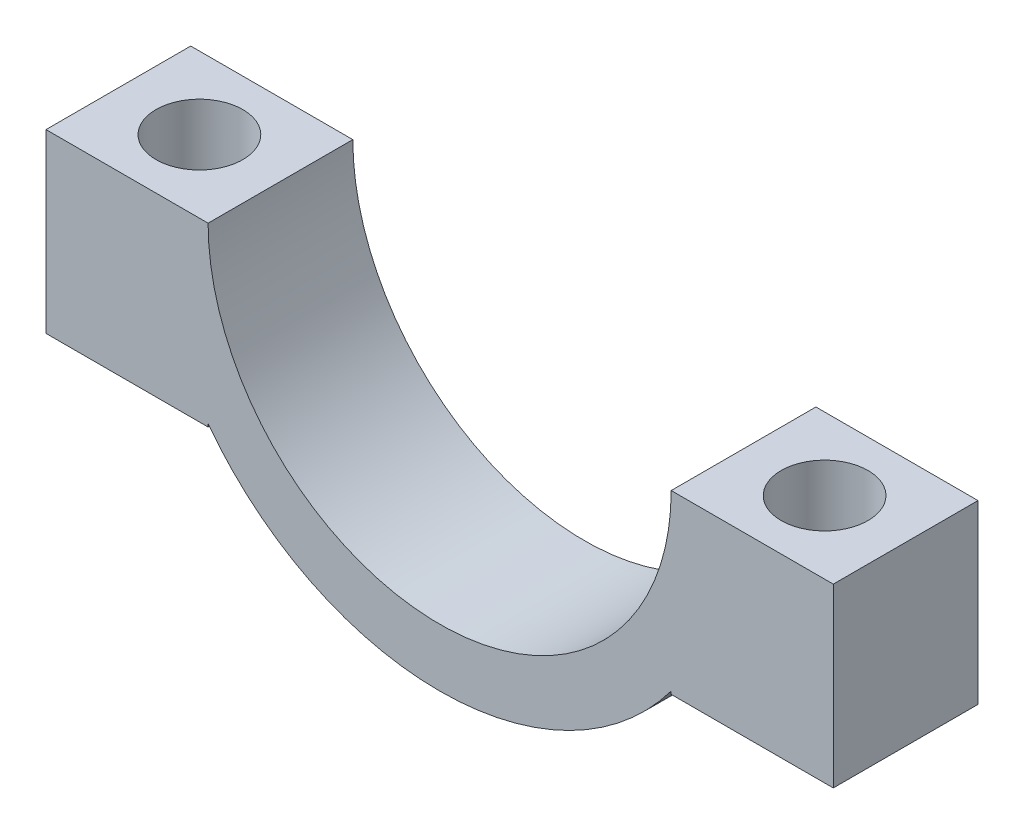
SolidWorks part; units mm, degrees
ref_plane "Front Plane" through (0, 0, 0) normal (0, 0, 1) x (1, 0, 0)
ref_plane "Top Plane" through (0, 0, 0) normal (0, 1, 0) x (1, 0, 0)
ref_plane "Right Plane" through (0, 0, 0) normal (1, 0, 0) x (0, 0, -1)
sketch "Sketch2" plane through (0, 0, 0) normal (0, 0, 1) x (1, 0, 0)
  line L0 (-1000, 0) -> (49000, 0) construction
  line L1 (-8, 0) -> (-13.6, 0)
  line L2 (-13.6, 0) -> (-13.6, 10)
  line L3 (-13.6, 10) -> (-8, 10)
  line L4 (-8, 10) -> (-8, 0)
  line L5 (0, -1000) -> (0, 49000) construction
  line L6 (8, 0) -> (13.6, 0)
  line L7 (13.6, 0) -> (13.6, 10)
  line L8 (13.6, 10) -> (8, 10)
  line L9 (8, 10) -> (8, 0)
  line L11 (-13.6, 0) -> (-8, 0)
  line L12 (-13.6, 0) -> (-13.6, -6.1)
  line L13 (-13.6, -6.1) -> (-8, -6.1)
  line L14 (-8, 0) -> (-8, -6.1)
  line L15 (13.6, 0) -> (8, 0)
  line L16 (13.6, 0) -> (13.6, -6.1)
  line L17 (13.6, -6.1) -> (8, -6.1)
  line L18 (8, 0) -> (8, -6.1)
  circle A0 centre (0, 0) radius 8
  circle A1 centre (0, 0) radius 10
  circle A2 centre (-5.5966, 11.6315) radius 2.9079
  circle A3 centre (5.6058, 11.6315) radius 2.9079
  spline S0 degree 1 poles (-8, 10) (0, 10) knots 0 0 1 1
  dimension "D1" = 16
  dimension "D2" = 20
  dimension "D5" = 10
  dimension "D3" = 5.6
  dimension "D4" = 10
  dimension "D6" = 5.6
  dimension "D7" = 6.1
  dimension "D8" = 6.1
extrude "Boss-Extrude1" add sketch "Sketch2" along normal blind 5 contours A1 L11 L12 L13 L14 | L1 A1 L14 | L14 A1 L18 A0 | L18 A1 L6 | A1 L18 L17 L16 L15
sketch "Sketch3" plane through (0, 0, 0) normal (0, 1, 0) x (1, 0, 0)
  line L0 (-13.6, -5) -> (-13.6, 0) construction
  line L1 (-8, 0) -> (-13.6, 0) construction
  line L2 (8, 0) -> (13.6, 0) construction
  circle A0 centre (-10.8, -2.5) radius 1.5
  circle A1 centre (10.8, -2.5) radius 1.5
  point P3 (-13.6, -2.5)
  point P6 (-10.8, 0)
  point P13 (10.8, 0)
  dimension "D4" = 3
extrude "Cut-Extrude1" cut sketch "Sketch3" against normal blind 10
